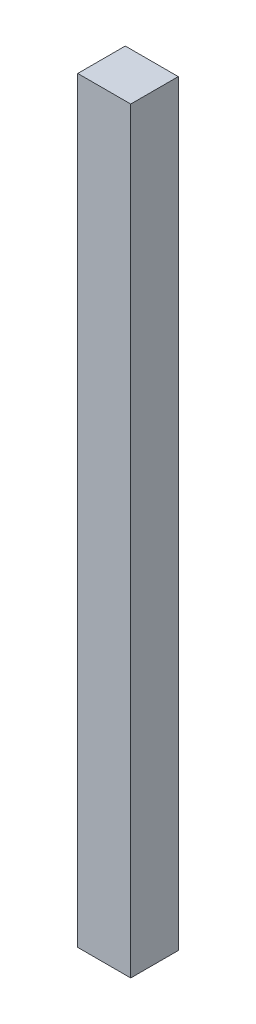
SolidWorks part; units mm, degrees
material "1023 al carbonio, lamiera (SS)"
ref_plane "Piano frontale" through (0, 0, 0) normal (0, 0, 1) x (1, 0, 0)
ref_plane "Piano superiore" through (0, 0, 0) normal (0, 1, 0) x (1, 0, 0)
ref_plane "Piano destro" through (0, 0, 0) normal (1, 0, 0) x (0, 0, -1)
sketch "Schizzo1" plane through (0, 0, 0) normal (0, 0, 1) x (1, 0, 0)
  line L0 (3.5, 100) -> (3.5, 0) construction
  line L1 (0, 0) -> (7, 0)
  line L2 (0, 0) -> (0, 100)
  line L3 (0, 100) -> (7, 100)
  line L4 (7, 0) -> (7, 100)
  dimension "D1" = 100
  dimension "D2" = 7
extrude "Estrusione-Estrusione1" add sketch "Schizzo1" along normal blind 6.28
